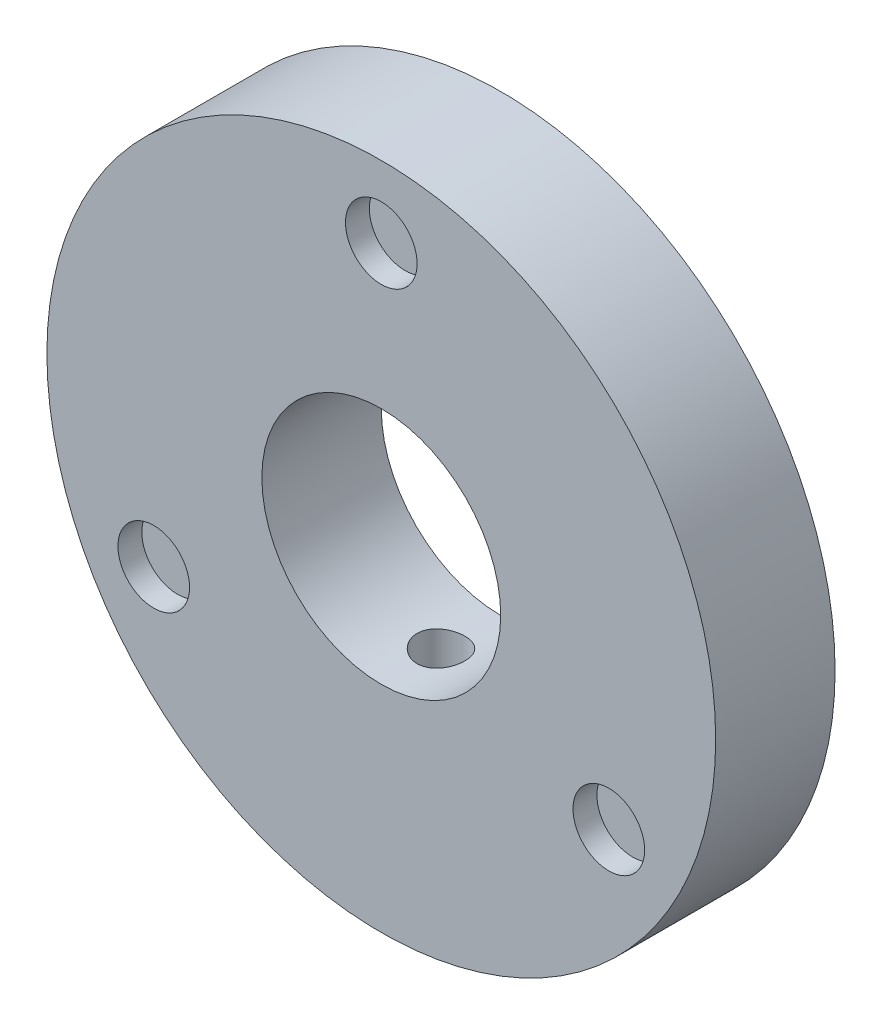
SolidWorks part; units mm, degrees
material "1060 Alloy"
ref_plane "Front Plane" through (0, 0, 0) normal (0, 0, 1) x (1, 0, 0)
ref_plane "Top Plane" through (0, 0, 0) normal (0, 1, 0) x (1, 0, 0)
ref_plane "Right Plane" through (0, 0, 0) normal (1, 0, 0) x (0, 0, -1)
sketch "Sketch3" plane through (0, 0, 0) normal (0, 0, 1) x (1, 0, 0)
  circle A0 centre (0, 0) radius 14
  circle A1 centre (0, 0) radius 5
  dimension "D1" = 10
  dimension "D2" = 28
extrude "Boss-Extrude1" add sketch "Sketch3" along normal blind 5
sketch "Sketch4" plane through (0, 0, 5) normal (0, 0, 1) x (1, 0, 0)
  circle A1 centre (0, 0) radius 11 construction
  circle A3 centre (0, 11) radius 1.5
  circle A4 centre (9.5263, -5.5) radius 1.5
  circle A5 centre (-9.5263, -5.5) radius 1.5
  point P10 (0, 0)
  dimension "D1" = 3
  dimension "D2" = 3
  dimension "D3" = 22
extrude "Cut-Extrude1" cut sketch "Sketch4" against normal blind 1
sketch "Sketch5" plane through (0, 0, 0) normal (0, 0, -1) x (-1, 0, 0)
  circle A0 centre (0, 0) radius 11 construction
  circle A2 centre (0, 11) radius 1.5
  circle A3 centre (9.5263, -5.5) radius 1.5
  circle A4 centre (-9.5263, -5.5) radius 1.5
  point P15 (0, 0)
  dimension "D1" = 3
  dimension "D2" = 3
  dimension "D3" = 22
extrude "Cut-Extrude2" cut sketch "Sketch5" against normal blind 1 contours A2 | A3 | A4
sketch "Sketch6" plane through (0, 0, 0) normal (0, 1, 0) x (1, 0, 0)
  circle A0 centre (0, -2.5) radius 1
  dimension "D2" = 2
  dimension "D1" = 2.5
extrude "Cut-Extrude3" cut sketch "Sketch6" against normal blind 30
